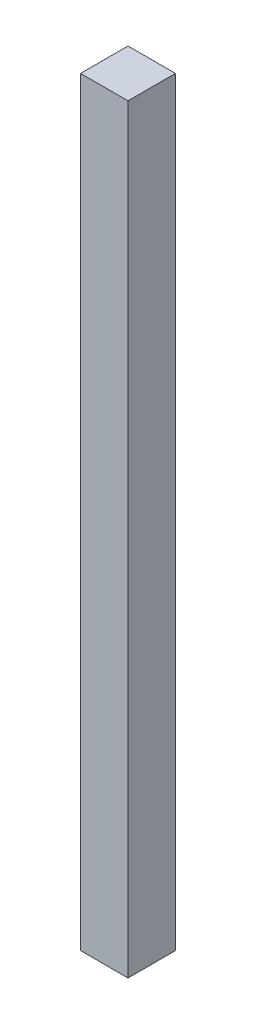
SolidWorks part; units mm, degrees
material "Commercially Pure CP-Ti UNS R50400 (SS)"
ref_plane "Front Plane" through (0, 0, 0) normal (0, 0, 1) x (1, 0, 0)
ref_plane "Top Plane" through (0, 0, 0) normal (0, 1, 0) x (1, 0, 0)
ref_plane "Right Plane" through (0, 0, 0) normal (1, 0, 0) x (0, 0, -1)
sketch "Sketch1" plane through (0, 0, 0) normal (0, 1, 0) x (1, 0, 0)
  line L1 (-10, -10) -> (10, -10)
  line L2 (-10, -10) -> (-10, 10)
  line L3 (-10, 10) -> (10, 10)
  line L4 (10, -10) -> (10, 10)
  line L5 (-10, -10) -> (10, 10) construction
  line L6 (-10, 10) -> (10, -10) construction
  point P0 (0, 0)
  dimension "D1" = 20
extrude "Boss-Extrude1" add sketch "Sketch1" along normal blind 320
